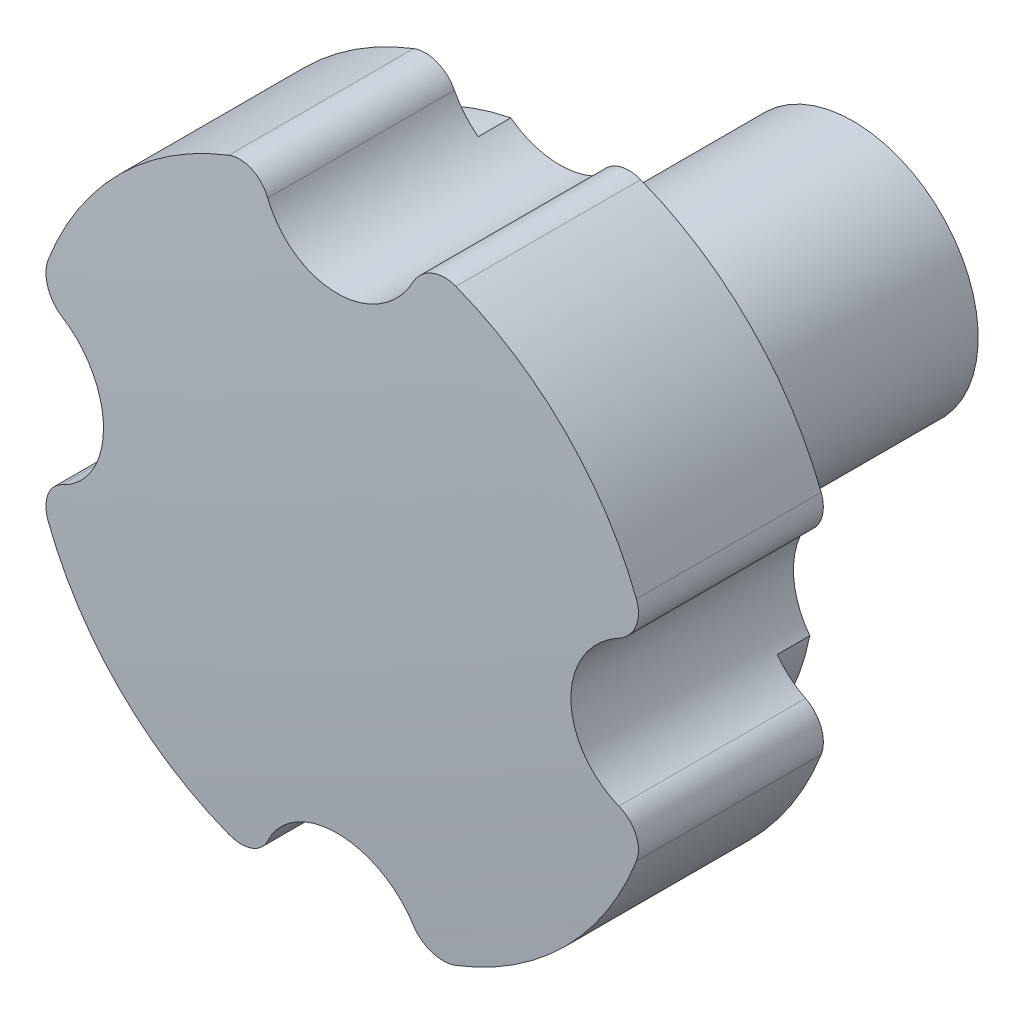
SolidWorks part; units mm, degrees
ref_plane "Front Plane" through (0, 0, 0) normal (0, 0, 1) x (1, 0, 0)
ref_plane "Top Plane" through (0, 0, 0) normal (0, 1, 0) x (1, 0, 0)
ref_plane "Right Plane" through (0, 0, 0) normal (1, 0, 0) x (0, 0, -1)
sketch "Sketch1" plane through (0, 0, 0) normal (0, 1, 0) x (1, 0, 0)
  line L0 (0, 358.8435) -> (0, -36.4755) construction
  line L1 (0, 18.0526) -> (0, 0)
  line L2 (-29, 1.0526) -> (-29, 18.0526)
  line L3 (-29, 18.0526) -> (-23.44, 18.0526)
  line L4 (-23.44, 18.0526) -> (-23.44, 21.0526)
  line L5 (-23.44, 21.0526) -> (-11.5, 21.0526)
  line L6 (-11.5, 21.0526) -> (-11.5, 48.0526)
  line L7 (-11.5, 48.0526) -> (-6, 48.0526)
  line L8 (-6, 48.0526) -> (-6, 18.0526)
  line L9 (-6, 18.0526) -> (0, 18.0526)
  arc A1 (-29, 1.0526) -> (0, 0) centre (0, 400) ccw
  dimension "D9" = 800
  dimension "D1" = 30
  dimension "D2" = 17
  dimension "D3" = 3
  dimension "D4" = 58
  dimension "D5" = 23
  dimension "D6" = 12
  dimension "D7" = 46.88
  dimension "D8" = 30
revolve "Revolve1" add sketch "Sketch1" angle 360 about L0
sketch "Sketch2" plane through (0, 0, 0) normal (0, 0, 1) x (1, 0, 0)
  circle A0 centre (0, 0) radius 29 construction
  circle A1 centre (0, 29) radius 7.5
  circle A2 centre (0, 0) radius 29 construction
  circle A3 centre (29, 0) radius 7.5
  circle A4 centre (0, 0) radius 29 construction
  circle A5 centre (0, -29) radius 7.5
  circle A6 centre (0, 0) radius 29 construction
  circle A7 centre (-29, 0) radius 7.5
  point P17 (0, 0)
  dimension "D1" = 58
  dimension "D2" = 15
  dimension "D3" = 4
extrude "Cut-Extrude1" cut sketch "Sketch2" against normal up to next
ref_plane "Plane1" through (0, 0, -18.0526) normal (0, 0, -1) x (-1, 0, 0)
sketch "Sketch3" plane through (0, 0, -18.0526) normal (0, 0, -1) x (-1, 0, 0)
  line L0 (0, 0) -> (-57.745, 57.745) construction
  line L1 (0, 0) -> (-62.0039, 0) construction
  dimension "D1" = 45
fillet "Fillet1" radius 3 8 edges at (-28.0302, -7.437, -9.5526) (-28.0302, 7.437, -9.5526) (7.437, -28.0302, -9.5526) (-7.437, -28.0302, -9.5526) (28.0302, 7.437, -9.5526) (28.0302, -7.437, -9.5526) (-7.437, 28.0302, -9.5526) (7.437, 28.0302, -9.5526)
sketch "Sketch4" plane through (0, 0, 0) normal (0, 1, 0) x (1, 0, 0)
  line L0 (0, 68.9802) -> (0, -14.4472) construction
sketch "Sketch5" plane through (0, 0, 0) normal (0, 0, 1) x (1, 0, 0)
  line L0 (0, 0) -> (-33.6671, 33.6671) construction
